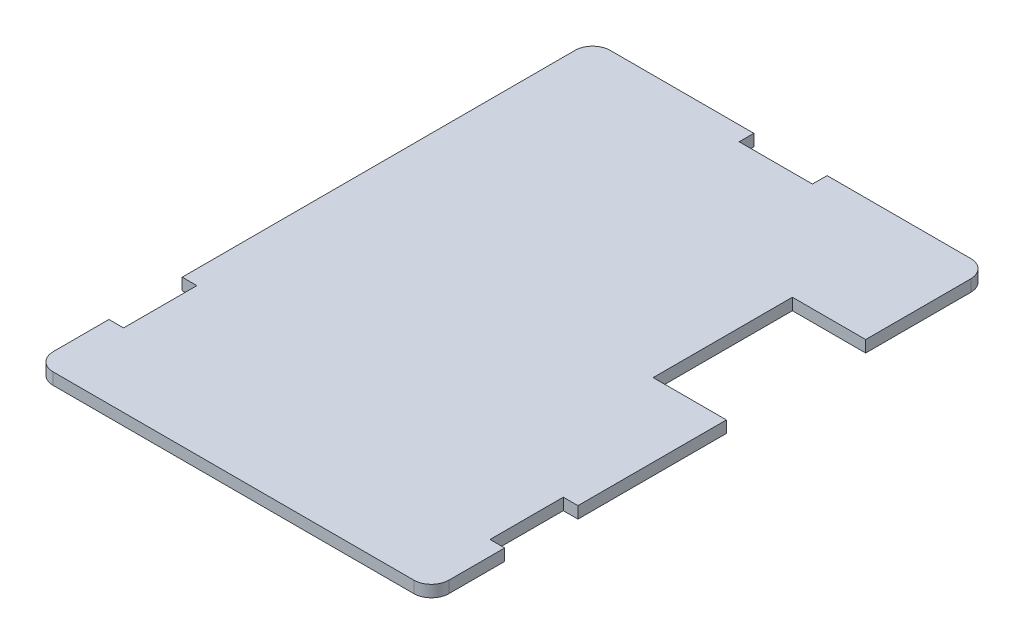
SolidWorks part; units mm, degrees
ref_plane "前视基准面" through (0, 0, 0) normal (0, 0, 1) x (1, 0, 0)
ref_plane "上视基准面" through (0, 0, 0) normal (0, 1, 0) x (1, 0, 0)
ref_plane "右视基准面" through (0, 0, 0) normal (1, 0, 0) x (0, 0, -1)
other "Configuration Table"
sketch "草图1" plane through (0, 0, 0) normal (0, 1, 0) x (1, 0, 0)
  line L1 (-13.5, -19) -> (13.5, -19)
  line L2 (-13.5, -19) -> (-13.5, 19)
  line L3 (-13.5, 19) -> (13.5, 19)
  line L4 (13.5, -19) -> (13.5, 19)
  line L5 (-13.5, -19) -> (13.5, 19) construction
  line L6 (-13.5, 19) -> (13.5, -19) construction
  point P0 (0, 0)
  dimension "D1" = 38
  dimension "D2" = 27
extrude "凸台-拉伸1" add sketch "草图1" along normal blind 0.8
fillet "圆角1" radius 1.2 4 edges at (13.5, 0.4, 19) (-13.5, 0.4, 19) (13.5, 0.4, -19) (-13.5, 0.4, -19)
sketch "草图2" plane through (0, 0.8, 0) normal (0, 1, 0) x (1, 0, 0)
  line L0 (13.5, -17.8) -> (13.5, 17.8) construction
  line L1 (13.5, 10.63) -> (8.5, 10.63)
  line L2 (13.5, 10.63) -> (13.5, 1.13)
  line L3 (13.5, 1.13) -> (8.5, 1.13)
  line L4 (8.5, 10.63) -> (8.5, 1.13)
  line L6 (-12.3, -19) -> (12.3, -19) construction
  dimension "D1" = 5
  dimension "D2" = 9.5
  dimension "D3" = 20.13
extrude "切除-拉伸1" cut sketch "草图2" against normal up to next
sketch "草图3" plane through (0, 0.8, 0) normal (0, 1, 0) x (1, 0, 0)
  line L0 (12.3, 19) -> (-12.3, 19) construction
  line L1 (-2.5, 19) -> (2.5, 19)
  line L2 (-2.5, 19) -> (-2.5, 18)
  line L3 (-2.5, 18) -> (2.5, 18)
  line L4 (2.5, 19) -> (2.5, 18)
  line L5 (-13.5, 17.8) -> (-13.5, -17.8) construction
  line L6 (-13.5, -9) -> (-12.5, -9)
  line L7 (-13.5, -9) -> (-13.5, -14)
  line L8 (-13.5, -14) -> (-12.5, -14)
  line L9 (-12.5, -9) -> (-12.5, -14)
  line L10 (13.5, -17.8) -> (13.5, 1.13) construction
  line L11 (13.5, -9) -> (12.5, -9)
  line L12 (13.5, -9) -> (13.5, -14)
  line L13 (13.5, -14) -> (12.5, -14)
  line L14 (12.5, -9) -> (12.5, -14)
  line L15 (-12.3, -19) -> (12.3, -19) construction
  point P20 (0, 19)
  point P21 (0, 19)
  dimension "D1" = 1
  dimension "D2" = 1
  dimension "D3" = 5
  dimension "D4" = 5
  dimension "D5" = 5
  dimension "D6" = 5
  dimension "D7" = 1
  dimension "D8" = 5
extrude "切除-拉伸2" cut sketch "草图3" against normal blind 10
